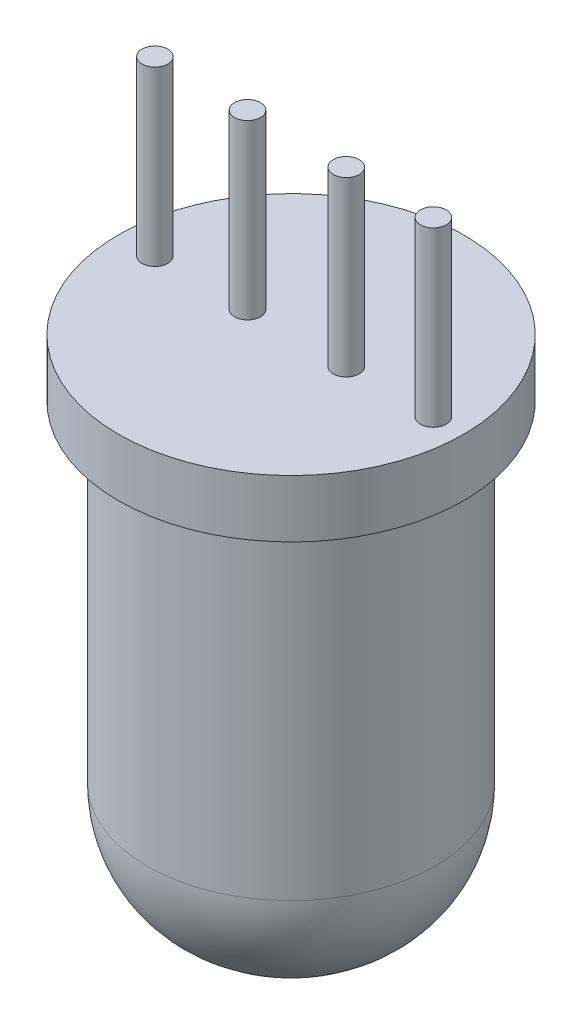
SolidWorks part; units mm, degrees
ref_plane "Front Plane" through (0, 0, 0) normal (0, 0, 1) x (1, 0, 0)
ref_plane "Top Plane" through (0, 0, 0) normal (0, 1, 0) x (1, 0, 0)
ref_plane "Right Plane" through (0, 0, 0) normal (1, 0, 0) x (0, 0, -1)
sketch "Sketch1" plane through (0, 0, 0) normal (0, 1, 0) x (1, 0, 0)
  circle A0 centre (0, 0) radius 2.5
  dimension "D1" = 5
extrude "Boss-Extrude1" add sketch "Sketch1" along normal blind 9
sketch "Sketch2" plane through (0, 9, 0) normal (0, 1, 0) x (1, 0, 0)
  circle A0 centre (0, 0) radius 3
  dimension "D1" = 6
extrude "Boss-Extrude3" add sketch "Sketch2" against normal blind 1
fillet "Fillet3" radius 2.25 1 edges at (0, 0, 2.5)
sketch "Sketch4" plane through (0, 9, 0) normal (0, 1, 0) x (1, 0, 0)
  circle A0 centre (-2.3661, 0) radius 0.2249
  circle A1 centre (-0.7567, 0) radius 0.2249
  circle A2 centre (0.9592, 0) radius 0.2249
  circle A3 centre (2.4726, 0) radius 0.2249
extrude "Boss-Extrude4" add sketch "Sketch4" along normal blind 3
